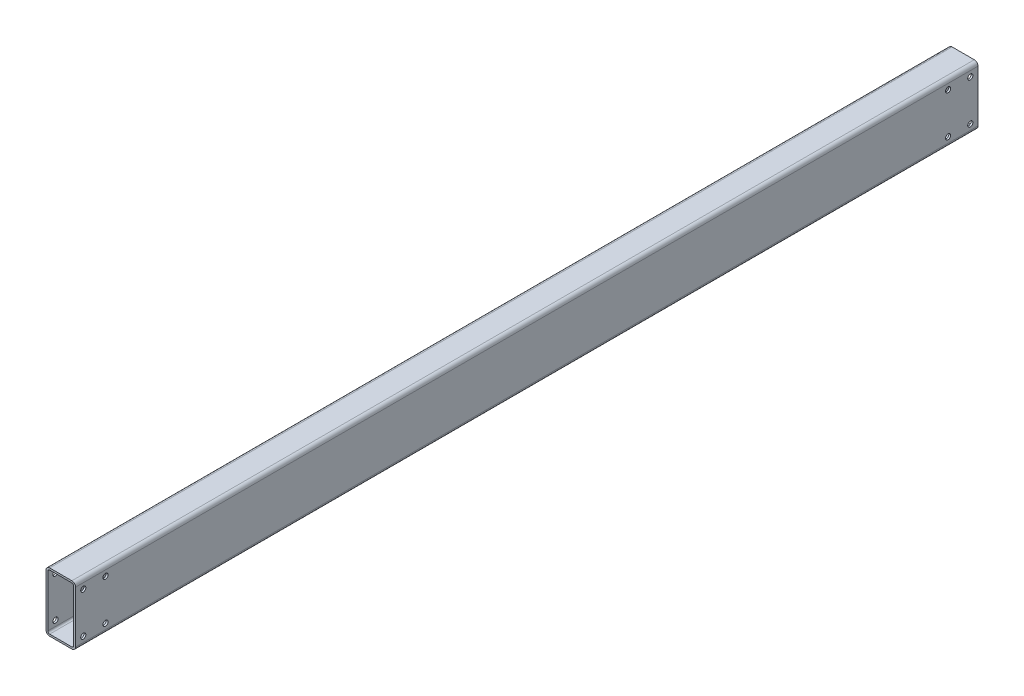
SolidWorks part; units mm, degrees
material "Plain Carbon Steel"
ref_plane "Front Plane" through (0, 0, 0) normal (0, 0, 1) x (1, 0, 0)
ref_plane "Top Plane" through (0, 0, 0) normal (0, 1, 0) x (1, 0, 0)
ref_plane "Right Plane" through (0, 0, 0) normal (1, 0, 0) x (0, 0, -1)
sketch "Sketch1" plane through (0, 0, 0) normal (0, 0, 1) x (1, 0, 0)
  line L0 (-17.5, -35) -> (-17.5, 35)
  line L1 (-15, -40) -> (15, -40)
  line L2 (-20, -35) -> (-20, 35)
  line L3 (-15, 40) -> (15, 40)
  line L4 (20, -35) -> (20, 35)
  line L5 (-20, -40) -> (20, 40) construction
  line L6 (-20, 40) -> (20, -40) construction
  line L7 (-15, 37.5) -> (15, 37.5)
  line L8 (17.5, -35) -> (17.5, 35)
  line L9 (-15, -37.5) -> (15, -37.5)
  arc A0 (15, -40) -> (20, -35) centre (15, -35) ccw
  arc A1 (-15, -40) -> (-20, -35) centre (-15, -35) cw
  arc A2 (15, 40) -> (20, 35) centre (15, 35) cw
  arc A3 (-20, 35) -> (-15, 40) centre (-15, 35) cw
  arc A4 (-17.5, 35) -> (-15, 37.5) centre (-15, 35) cw
  arc A5 (15, 37.5) -> (17.5, 35) centre (15, 35) cw
  arc A6 (15, -37.5) -> (17.5, -35) centre (15, -35) ccw
  arc A7 (-15, -37.5) -> (-17.5, -35) centre (-15, -35) cw
  point P0 (0, 0)
  dimension "D3" = 5
  dimension "3\"" = 80
  dimension "D2" = 40
  dimension "D4" = 2.5
extrude "Boss-Extrude1" add sketch "Sketch1" along normal blind 1220
sketch "Sketch2" plane through (-20, 0, 0) normal (-1, 0, 0) x (0, 0, 1)
  line L0 (0, 35) -> (0, -35) construction
  line L1 (0, 40) -> (50.8, 40) construction
  line L2 (0, 40) -> (0, -40) construction
  line L3 (0, -40) -> (50.8, -40) construction
  line L4 (50.8, 40) -> (50.8, -40) construction
  line L5 (1220, 40) -> (0, 40) construction
  line L6 (1220, -40) -> (0, -40) construction
  line L7 (0, 0) -> (50.8, 0) construction
  line L9 (10.4, -27.5) -> (40.4, -27.5) construction
  line L10 (10.4, -27.5) -> (10.4, 27.5) construction
  line L11 (10.4, 27.5) -> (40.4, 27.5) construction
  line L12 (40.4, -27.5) -> (40.4, 27.5) construction
  line L13 (10.4, -27.5) -> (40.4, 27.5) construction
  line L14 (10.4, 27.5) -> (40.4, -27.5) construction
  circle A0 centre (10.4, 27.5) radius 3.5
  circle A1 centre (40.4, 27.5) radius 3.5
  circle A2 centre (40.4, -27.5) radius 3.5
  circle A3 centre (10.4, -27.5) radius 3.5
  point P13 (25.4, 0)
  dimension "D2" = 7
  dimension "D1" = 50.8
  dimension "D3" = 55
  dimension "D4" = 30
extrude "Cut-Extrude1" cut sketch "Sketch2" against normal through all
ref_plane "Plane1" through (0, 0, 610) normal (0, 0, 1) x (1, 0, 0)
mirror "Mirror1" about plane through (0, 0, 610) normal (0, 0, 1) of "Cut-Extrude1"
equation "\"tube height\"= \"3\"@Sketch1\""
equation "\"tube width\"= \"D2@Sketch1\""
equation "\"tube thickness\"= \"D4@Sketch1\""
equation "\"tube radius\"= \"D4@Sketch1\""
